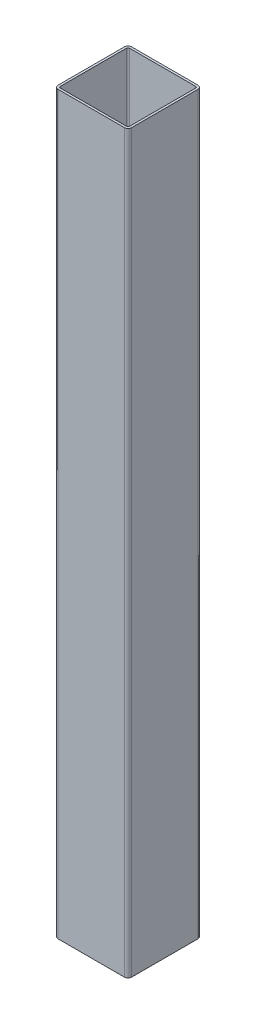
SolidWorks part; units mm, degrees
ref_plane "Спереди" through (0, 0, 0) normal (0, 0, 1) x (1, 0, 0)
ref_plane "Сверху" through (0, 0, 0) normal (0, 1, 0) x (1, 0, 0)
ref_plane "Справа" through (0, 0, 0) normal (1, 0, 0) x (0, 0, -1)
sketch "Эскиз1" plane through (0, 0, 0) normal (0, 1, 0) x (1, 0, 0)
  line L1 (-45, 50) -> (45, 50)
  line L2 (-50, 45) -> (-50, -45)
  line L3 (-45, -50) -> (45, -50)
  line L4 (50, 45) -> (50, -45)
  line L5 (-50, 50) -> (50, -50) construction
  line L6 (-50, -50) -> (50, 50) construction
  arc A0 (45, -50) -> (50, -45) centre (45, -45) ccw
  arc A1 (45, 50) -> (50, 45) centre (45, 45) cw
  arc A2 (-45, 50) -> (-50, 45) centre (-45, 45) ccw
  arc A3 (-50, -45) -> (-45, -50) centre (-45, -45) ccw
  point P0 (0, 0)
  dimension "D3" = 5
  dimension "D1" = 100
  dimension "D2" = 100
extrude "Вытянуть-Тонкостенный1" add sketch "Эскиз1" along normal blind 1000 thin
